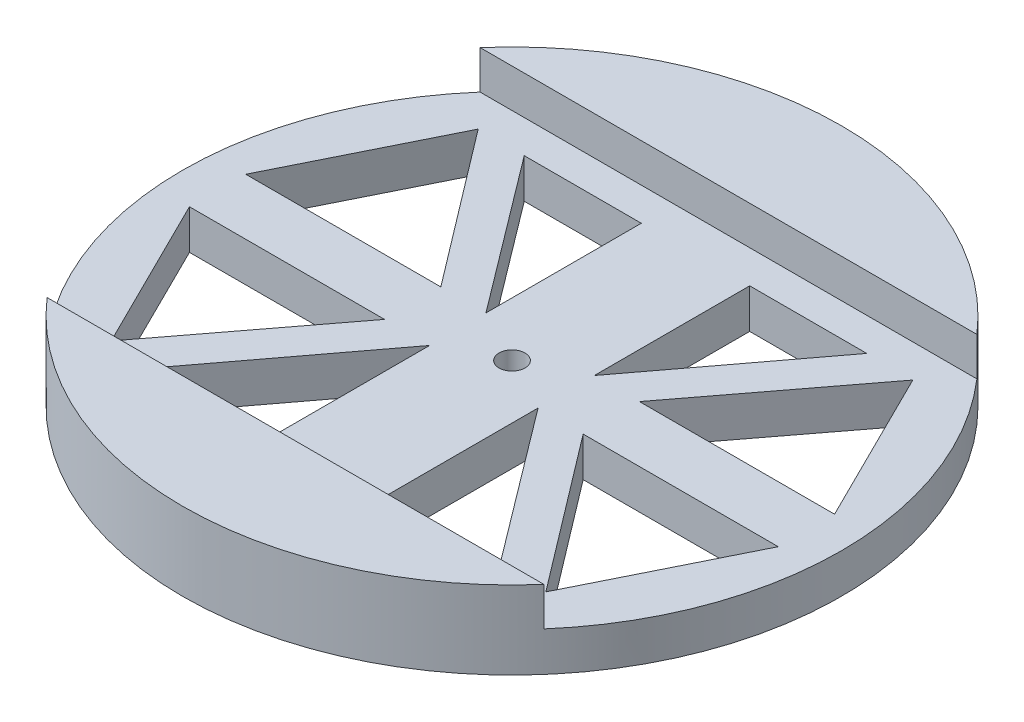
SolidWorks part; units mm, degrees
ref_plane "Front Plane" through (0, 0, 0) normal (0, 0, 1) x (1, 0, 0)
ref_plane "Top Plane" through (0, 0, 0) normal (0, 1, 0) x (1, 0, 0)
ref_plane "Right Plane" through (0, 0, 0) normal (1, 0, 0) x (0, 0, -1)
sketch "Sketch1" plane through (0, 0, 0) normal (0, 1, 0) x (1, 0, 0)
  circle A0 centre (0, 0) radius 76
  dimension "D1" = 152
extrude "Boss-Extrude1" add sketch "Sketch1" along normal blind 18 contours A0
sketch "Sketch2" plane through (0, 18, 0) normal (0, 1, 0) x (1, 0, 0)
  line L0 (-76, 0) -> (76, 0) construction
  line L1 (-58.008, 0) -> (58.008, 0) construction
  line L2 (-58.008, 49.9318) -> (58.008, 49.9318)
  line L3 (-58.008, -49.9318) -> (58.008, -49.9318)
  circle A0 centre (0, 0) radius 76 construction
  arc A1 (-58.008, 49.9318) -> (-58.008, -49.9318) centre (-58.008, 0) ccw
  arc A2 (58.008, -49.9318) -> (58.008, 49.9318) centre (58.008, 0) ccw
  point P7 (0, 0)
extrude "Cut-Extrude4" cut sketch "Sketch2" against normal blind 8.89
sketch "Sketch5" plane through (0, 9.11, 0) normal (0, 1, 0) x (1, 0, 0)
  line L0 (0, 3) -> (0, -3)
  circle A0 centre (0, 0) radius 3
extrude "Cut-Extrude5" cut sketch "Sketch5" against normal blind 20 contours A0
sketch "Sketch7" plane through (0, 9.11, 0) normal (0, 1, 0) x (1, 0, 0)
  line L0 (-50.1251, 42.3228) -> (-67.9029, 6.4906)
  line L1 (-67.9029, 6.4906) -> (-22.9029, 6.4906)
  line L2 (-22.9029, 6.4906) -> (-50.1251, 42.3228)
  line L3 (0, 49.9318) -> (0, -49.9318) construction
  line L4 (57.2959, 49.9318) -> (-57.2959, 49.9318) construction
  line L5 (-57.2959, -49.9318) -> (57.2959, -49.9318) construction
  line L6 (67.9029, 6.4906) -> (22.9029, 6.4906)
  line L7 (50.1251, 42.3228) -> (67.9029, 6.4906)
  line L8 (22.9029, 6.4906) -> (50.1251, 42.3228)
  line L9 (-76, 0) -> (76, 0) construction
  line L10 (50.1251, -42.3228) -> (67.9029, -6.4906)
  line L11 (22.9029, -6.4906) -> (50.1251, -42.3228)
  line L12 (67.9029, -6.4906) -> (22.9029, -6.4906)
  line L13 (-67.9029, -6.4906) -> (-22.9029, -6.4906)
  line L14 (-50.1251, -42.3228) -> (-67.9029, -6.4906)
  line L15 (-22.9029, -6.4906) -> (-50.1251, -42.3228)
  arc A0 (-57.2959, 49.9318) -> (-57.2959, -49.9318) centre (0, 0) ccw construction
  arc A1 (57.2959, -49.9318) -> (57.2959, 49.9318) centre (0, 0) ccw construction
  dimension "D1" = 40
  dimension "D2" = 45
  dimension "D3" = 45
extrude "Cut-Extrude6" cut sketch "Sketch7" against normal through all
sketch "Sketch9" plane through (0, 9.11, 0) normal (0, 1, 0) x (1, 0, 0)
  line L0 (-12.5, 6.4906) -> (-12.5, 42.3228)
  line L1 (-12.5, 42.3228) -> (-39.5, 42.3228)
  line L2 (-12.5, 6.4906) -> (-39.5, 42.3228)
  line L3 (0, 49.9318) -> (0, -49.9318) construction
  line L4 (57.2959, 49.9318) -> (-57.2959, 49.9318) construction
  line L5 (-57.2959, -49.9318) -> (57.2959, -49.9318) construction
  line L6 (-76, 0) -> (76, 0) construction
  line L7 (12.5, 6.4906) -> (39.5, 42.3228)
  line L8 (12.5, 42.3228) -> (39.5, 42.3228)
  line L9 (12.5, 6.4906) -> (12.5, 42.3228)
  line L10 (12.5, -6.4906) -> (12.5, -42.3228)
  line L11 (12.5, -42.3228) -> (39.5, -42.3228)
  line L12 (12.5, -6.4906) -> (39.5, -42.3228)
  line L13 (-12.5, -6.4906) -> (-39.5, -42.3228)
  line L14 (-12.5, -42.3228) -> (-39.5, -42.3228)
  line L15 (-12.5, -6.4906) -> (-12.5, -42.3228)
  arc A0 (-57.2959, 49.9318) -> (-57.2959, -49.9318) centre (0, 0) ccw construction
  arc A1 (57.2959, -49.9318) -> (57.2959, 49.9318) centre (0, 0) ccw construction
  dimension "D1" = 27
  dimension "D2" = 12.5
  dimension "D3" = 27
extrude "Cut-Extrude7" cut sketch "Sketch9" against normal through all
sketch "Sketch10" plane through (0, 9.11, 0) normal (0, 1, 0) x (1, 0, 0)
  line L0 (-22.9029, 6.4906) -> (-50.1251, 42.3228) construction
  line L1 (-39.5, 42.3228) -> (-12.5, 6.4906) construction
  dimension "D1" = 16.5359
